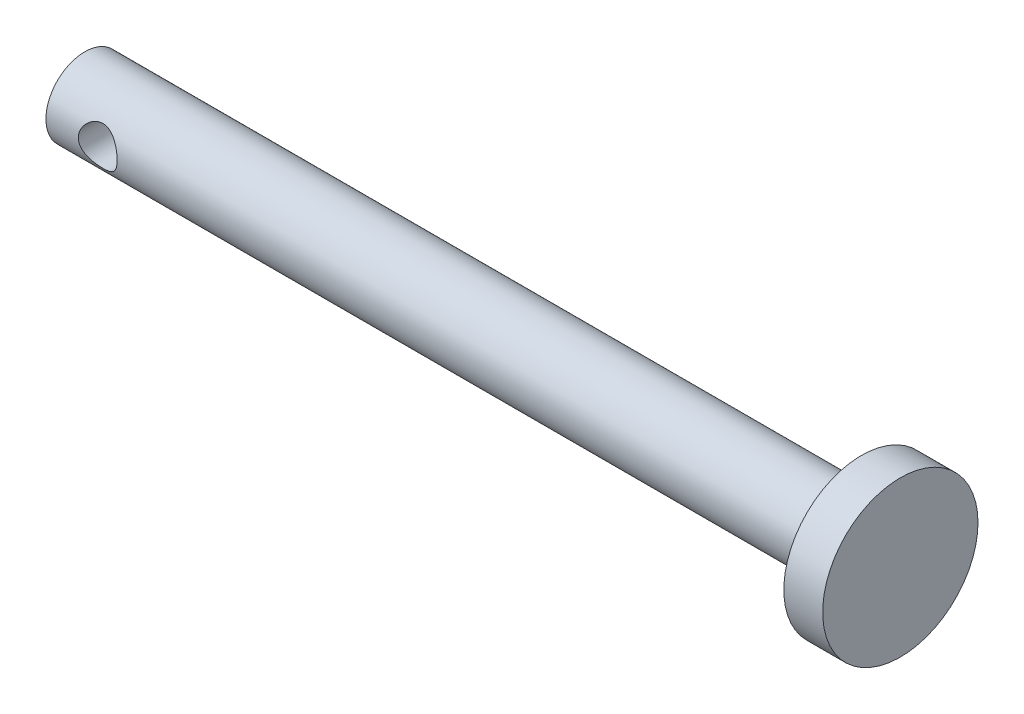
SolidWorks part; units mm, degrees
ref_plane "Front Plane" through (0, 0, 0) normal (0, 0, 1) x (1, 0, 0)
ref_plane "Top Plane" through (0, 0, 0) normal (0, 1, 0) x (1, 0, 0)
ref_plane "Right Plane" through (0, 0, 0) normal (1, 0, 0) x (0, 0, -1)
sketch "Sketch1" plane through (0, 0, 0) normal (1, 0, 0) x (0, 0, -1)
  circle A0 centre (0, 0) radius 3
  dimension "D1" = 6
extrude "Boss-Extrude1" add sketch "Sketch1" along normal blind 60
sketch "Sketch2" plane through (60, 0, 0) normal (1, 0, 0) x (0, 0, -1)
  circle A0 centre (0, 0) radius 6
  dimension "D1" = 12
extrude "Boss-Extrude2" add sketch "Sketch2" along normal blind 3
sketch "Sketch3" plane through (0, 0, 0) normal (0, 0, 1) x (1, 0, 0)
  line L0 (6.6, 0) -> (-6.6, 0) construction
  line L1 (0, -6.6) -> (0, 6.6) construction
  circle A0 centre (4, 0) radius 1.5
  dimension "D1" = 3
  dimension "D2" = 4
extrude "Cut-Extrude1" cut sketch "Sketch3" against normal through all both and the other way through all
chamfer "Chamfer1" [suppressed] distance 0.5 angle 45
sketch "Sketch4" plane through (0, 0, 0) normal (-1, 0, 0) x (0, 0, 1)
  circle A0 centre (0, 0) radius 6
extrude "Boss-Extrude3" [suppressed] add sketch "Sketch4" along normal blind 3
chamfer "Chamfer2" [suppressed] distance 0.5 angle 45
